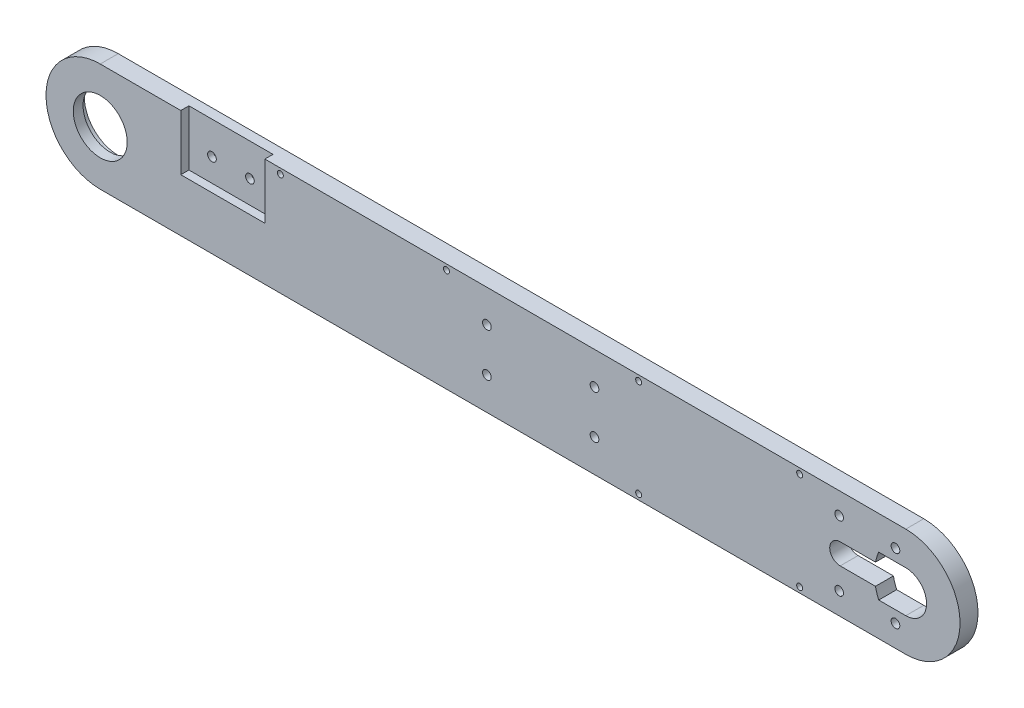
SolidWorks part; units mm, degrees
ref_plane "Front Plane" through (0, 0, 0) normal (0, 0, 1) x (1, 0, 0)
ref_plane "Top Plane" through (0, 0, 0) normal (0, 1, 0) x (1, 0, 0)
ref_plane "Right Plane" through (0, 0, 0) normal (1, 0, 0) x (0, 0, -1)
sketch "Sketch1" plane through (0, 0, 0) normal (0, 0, 1) x (1, 0, 0)
  line L0 (-53.15, -20.3675) -> (-350.15, -20.3675)
  line L1 (-350.15, 19.6325) -> (-53.15, 19.6325)
  arc A0 (-350.15, -20.3675) -> (-350.15, 19.6325) centre (-350.15, -0.3675) cw
  arc A1 (-53.15, 19.6325) -> (-53.15, -20.3675) centre (-53.15, -0.3675) cw
  dimension "D1" = 20
  dimension "D2" = 297
extrude "Boss-Extrude1" add sketch "Sketch1" along normal blind 6.62
sketch "Sketch2" plane through (0, 0, 0) normal (0, 0, -1) x (-1, 0, 0)
  line L0 (53.15, -0.3675) -> (45.5, -0.3675) construction
  line L1 (53.15, -0.3675) -> (77.35, -0.3675) construction
  line L2 (53.15, 7.2825) -> (63.133, 7.2825)
  line L3 (53.15, -8.0175) -> (63.133, -8.0175)
  line L4 (53.15, 19.6325) -> (350.15, 19.6325) construction
  line L5 (77.35, 3.4825) -> (64.3315, 3.4825)
  line L6 (77.35, -4.2175) -> (64.3315, -4.2175)
  line L7 (45.5, -0.3675) -> (45.5, 4.4582) construction
  line L8 (81.2, -0.3675) -> (81.2, 3.7385) construction
  arc A0 (53.15, 7.2825) -> (53.15, -8.0175) centre (53.15, -0.3675) ccw
  arc A1 (63.133, -8.0175) -> (64.3315, -4.2175) centre (45.5, -0.3675) ccw
  arc A2 (77.35, -4.2175) -> (77.35, 3.4825) centre (77.35, -0.3675) ccw
  arc A3 (64.3315, 3.4825) -> (63.133, 7.2825) centre (45.5, -0.3675) ccw
  point P5 (58.15, -0.3675)
  dimension "D2" = 7.65
  dimension "D3" = 7.7
  dimension "D4" = 35.7
extrude "Cut-Extrude1" cut sketch "Sketch2" against normal up to next
sketch "Sketch3" plane through (0, 0, 0) normal (0, 0, -1) x (-1, 0, 0)
  circle A0 centre (77.7155, -12.3675) radius 1.6
  circle A1 centre (77.7155, 11.6325) radius 1.6
  circle A2 centre (56.9655, 11.6325) radius 1.6
  circle A3 centre (56.9655, -12.3675) radius 1.6
extrude "Cut-Extrude2" cut sketch "Sketch3" against normal up to next
sketch "Sketch4" plane through (0, 0, 0) normal (0, 0, -1) x (-1, 0, 0)
  circle A0 centre (56.9655, 11.6325) radius 2.75
  circle A1 centre (77.7155, 11.6325) radius 2.75
  circle A2 centre (77.7155, -12.3675) radius 2.75
  circle A3 centre (56.9655, -12.3675) radius 2.75
  dimension "D1" = 5.5
extrude "Cut-Extrude3" cut sketch "Sketch4" against normal blind 3.2
sketch "Sketch5" plane through (0, 0, 0) normal (0, 0, -1) x (-1, 0, 0)
  line L0 (337.15, 19.6325) -> (337.15, -20.3675)
  line L1 (53.15, 19.6325) -> (350.15, 19.6325) construction
  line L2 (350.15, -20.3675) -> (53.15, -20.3675) construction
  line L3 (337.15, -20.3675) -> (370.15, -20.3675)
  line L4 (370.15, -20.3675) -> (370.15, 19.6325)
  line L5 (370.15, 19.6325) -> (337.15, 19.6325)
  arc A0 (350.15, -20.3675) -> (350.15, 19.6325) centre (350.15, -0.3675) ccw construction
  arc A1 (53.15, 19.6325) -> (53.15, -20.3675) centre (53.15, -0.3675) ccw construction
  dimension "D1" = 284
sketch "Sketch6" plane through (0, 0, 6.62) normal (0, 0, 1) x (1, 0, 0)
  circle A0 centre (-350.15, -0.3675) radius 9.95
  dimension "D1" = 19.9
extrude "Cut-Extrude4" cut sketch "Sketch6" against normal blind 10
sketch "Sketch7" plane through (0, 0, 0) normal (0, 0, -1) x (-1, 0, 0)
  circle A0 centre (350.15, -0.3675) radius 12.5
  dimension "D1" = 25
extrude "Cut-Extrude5" cut sketch "Sketch7" against normal blind 3
sketch "Sketch9" plane through (0, 0, 6.62) normal (0, 0, 1) x (1, 0, 0)
  line L0 (-328.15, -20.3675) -> (-328.15, 26.8232)
  line L1 (-350.15, -20.3675) -> (-53.15, -20.3675) construction
  line L2 (-328.15, 26.8232) -> (-375.5796, 26.8232)
  line L3 (-375.5796, 26.8232) -> (-375.5796, -27.8433)
  line L4 (-375.5796, -27.8433) -> (-328.15, -27.8433)
  line L5 (-328.15, -27.8433) -> (-328.15, -20.3675)
  circle A0 centre (-350.15, -0.3675) radius 9.95 construction
  dimension "D1" = 22
extrude "Cut-Extrude8" [suppressed] cut sketch "Sketch9" against normal blind 3
sketch "Sketch10" plane through (0, 0, 6.62) normal (0, 0, 1) x (1, 0, 0)
  circle A0 centre (-207.5905, -8.3675) radius 1.6
  circle A1 centre (-207.5905, 7.6325) radius 1.6
  circle A2 centre (-167.9179, -8.3675) radius 1.6
  circle A3 centre (-167.9179, 7.6325) radius 1.6
extrude "Cut-Extrude9" cut sketch "Sketch10" against normal up to next
sketch "Sketch11" plane through (0, 0, 0) normal (0, 0, -1) x (-1, 0, 0)
  circle A0 centre (207.5905, 7.6325) radius 2.75
  circle A1 centre (207.5905, -8.3675) radius 2.75
  circle A2 centre (167.9179, 7.6325) radius 2.75
  circle A3 centre (167.9179, -8.3675) radius 2.75
  dimension "D1" = 5.5
extrude "Cut-Extrude10" cut sketch "Sketch11" against normal blind 3
sketch "Sketch12" plane through (0, 0, 6.62) normal (0, 0, 1) x (1, 0, 0)
  line L0 (-320.4571, 19.6325) -> (-320.4571, -0.8675)
  line L1 (-53.15, 19.6325) -> (-350.15, 19.6325) construction
  line L2 (-320.4571, -0.8675) -> (-289.4571, -0.8675)
  line L3 (-289.4571, -0.8675) -> (-289.4571, 19.6325)
  line L4 (-289.4571, 19.6325) -> (-320.4571, 19.6325)
  line L5 (-319.9571, -0.3675) -> (-289.9571, -0.3675) construction
  line L6 (-319.9571, -0.3675) -> (-319.9571, 11.6325) construction
  line L7 (-289.9571, -0.3675) -> (-289.9571, 11.6325) construction
  dimension "D1" = 0.5
  dimension "D2" = 0.5
  dimension "D3" = 0.5
extrude "Cut-Extrude11" cut sketch "Sketch12" against normal blind 3
sketch "Sketch13" plane through (0, 0, 6.62) normal (0, 0, 1) x (1, 0, 0)
  circle A1 centre (-311.9571, 7.6325) radius 1.6
  circle A2 centre (-297.9571, 7.6325) radius 1.6
extrude "Cut-Extrude12" cut sketch "Sketch13" against normal up to next
sketch "Sketch14" plane through (0, 0, 0) normal (0, 0, -1) x (-1, 0, 0)
  circle A0 centre (311.9571, 7.6325) radius 2.75
  circle A1 centre (297.9571, 7.6325) radius 2.75
  dimension "D1" = 5.5
extrude "Cut-Extrude13" cut sketch "Sketch14" against normal blind 1.5
sketch "Sketch15" plane through (0, 0, 6.62) normal (0, 0, 1) x (1, 0, 0)
  line L0 (-350.15, -20.3675) -> (-53.15, -20.3675) construction
  line L1 (-53.15, 19.6325) -> (-289.4571, 19.6325) construction
  circle A0 centre (-151.6445, -18.3675) radius 1.1
  circle A1 centre (-92.2804, -18.3675) radius 1.1
  circle A2 centre (-151.6445, 17.6325) radius 1.1
  circle A3 centre (-92.2804, 17.6325) radius 1.1
  circle A4 centre (-222.4916, 17.6325) radius 1.1
  circle A5 centre (-283.7505, 17.6325) radius 1.1
  dimension "D1" = 2.2
  dimension "D2" = 2
  dimension "D3" = 2
extrude "Cut-Extrude14" cut sketch "Sketch15" against normal up to next
